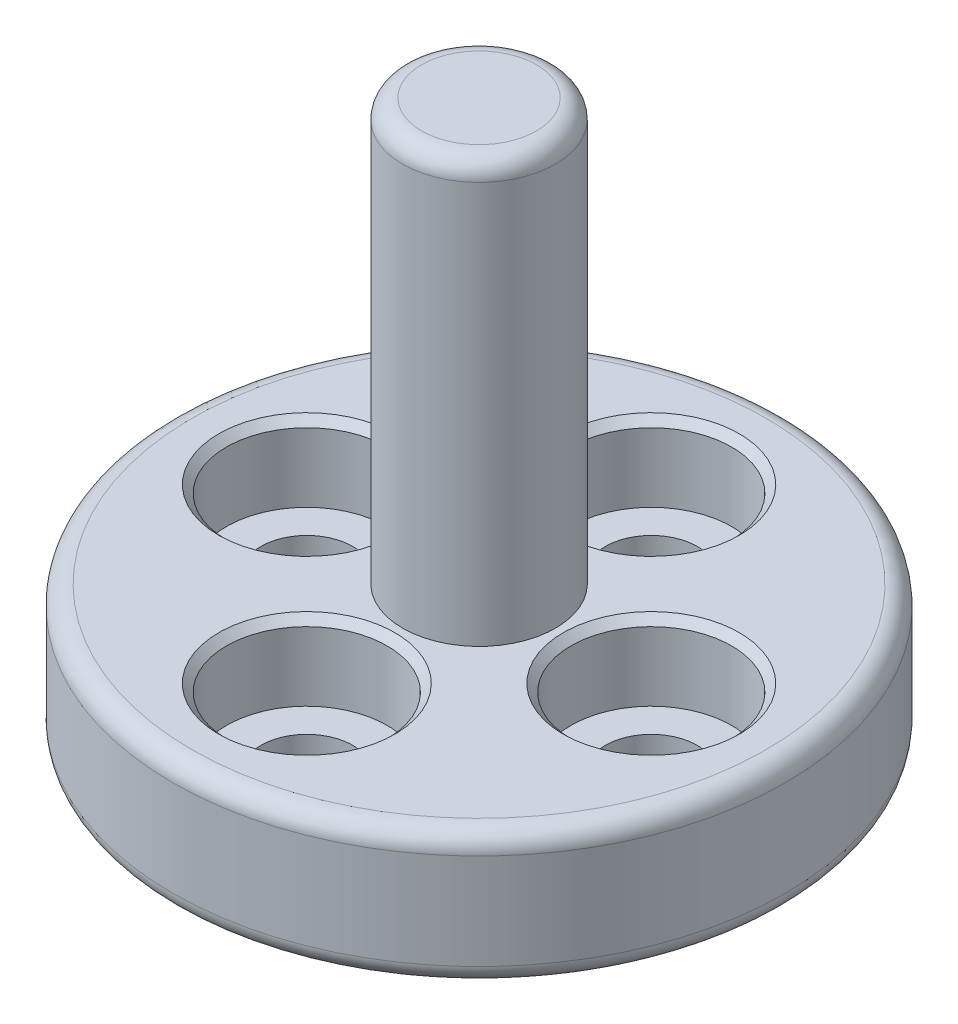
SolidWorks part; units mm, degrees
ref_plane "Front Plane" through (0, 0, 0) normal (0, 0, 1) x (1, 0, 0)
ref_plane "Top Plane" through (0, 0, 0) normal (0, 1, 0) x (1, 0, 0)
ref_plane "Right Plane" through (0, 0, 0) normal (1, 0, 0) x (0, 0, -1)
sketch "Sketch1" plane through (0, 0, 0) normal (0, 1, 0) x (1, 0, 0)
  circle A0 centre (0, 0) radius 8
  dimension "D1" = 16
extrude "Boss-Extrude1" add sketch "Sketch1" along normal blind 3.5
sketch "Sketch2" plane through (0, 3.5, 0) normal (0, 1, 0) x (1, 0, 0)
  circle A0 centre (0, 0) radius 2
  dimension "D1" = 4
extrude "Boss-Extrude2" add sketch "Sketch2" along normal blind 11
sketch "Sketch4" plane through (0, 3.5, 0) normal (0, 1, 0) x (1, 0, 0)
  circle A0 centre (0, 0) radius 4.5 construction
  circle A1 centre (0, 4.5) radius 1.2
  circle A2 centre (4.5, 0) radius 1.2
  circle A3 centre (0, -4.5) radius 1.2
  circle A4 centre (-4.5, 0) radius 1.2
  point P14 (0, 0)
  dimension "D1" = 9
  dimension "D2" = 2.4
  dimension "D3" = 4
extrude "Cut-Extrude1" cut sketch "Sketch4" against normal through all
sketch "Sketch5" plane through (0, 3.5, 0) normal (0, 1, 0) x (1, 0, 0)
  circle A0 centre (0, 4.5) radius 2.1
  circle A1 centre (4.5, 0) radius 2.1
  circle A2 centre (0, -4.5) radius 2.1
  circle A3 centre (-4.5, 0) radius 2.1
  point P12 (0, 0)
  dimension "D1" = 4.2
  dimension "D2" = 4
extrude "Cut-Extrude2" cut sketch "Sketch5" against normal blind 2
chamfer "Chamfer2" distance 0.2 angle 45 4 edges at (0, 3.5, 6.6) (4.5, 3.5, 2.1) (0, 3.5, -2.4) (-4.5, 3.5, 2.1)
fillet "Fillet3" radius 0.5 1 edges at (0, 14.5, 2)
fillet "Fillet4" radius 0.5 2 edges at (0, 0, 8) (0, 3.5, 8)
